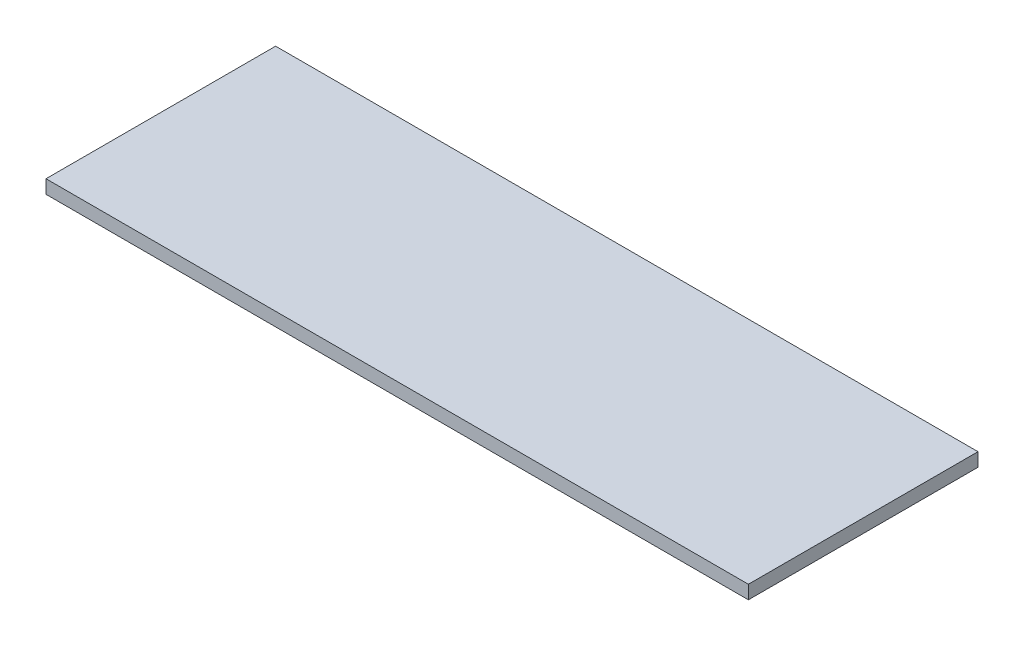
SolidWorks part; units mm, degrees
ref_plane "Front Plane" through (0, 0, 0) normal (0, 0, 1) x (1, 0, 0)
ref_plane "Top Plane" through (0, 0, 0) normal (0, 1, 0) x (1, 0, 0)
ref_plane "Right Plane" through (0, 0, 0) normal (1, 0, 0) x (0, 0, -1)
sketch "Sketch1" plane through (0, 0, 0) normal (0, 1, 0) x (1, 0, 0)
  line L1 (-29.0398, 1.6152) -> (22.9602, 1.6152)
  line L2 (-29.0398, 1.6152) -> (-29.0398, -15.3848)
  line L3 (-29.0398, -15.3848) -> (22.9602, -15.3848)
  line L4 (22.9602, 1.6152) -> (22.9602, -15.3848)
  dimension "D1" = 17
  dimension "D2" = 52
extrude "Boss-Extrude1" add sketch "Sketch1" along normal blind 1
